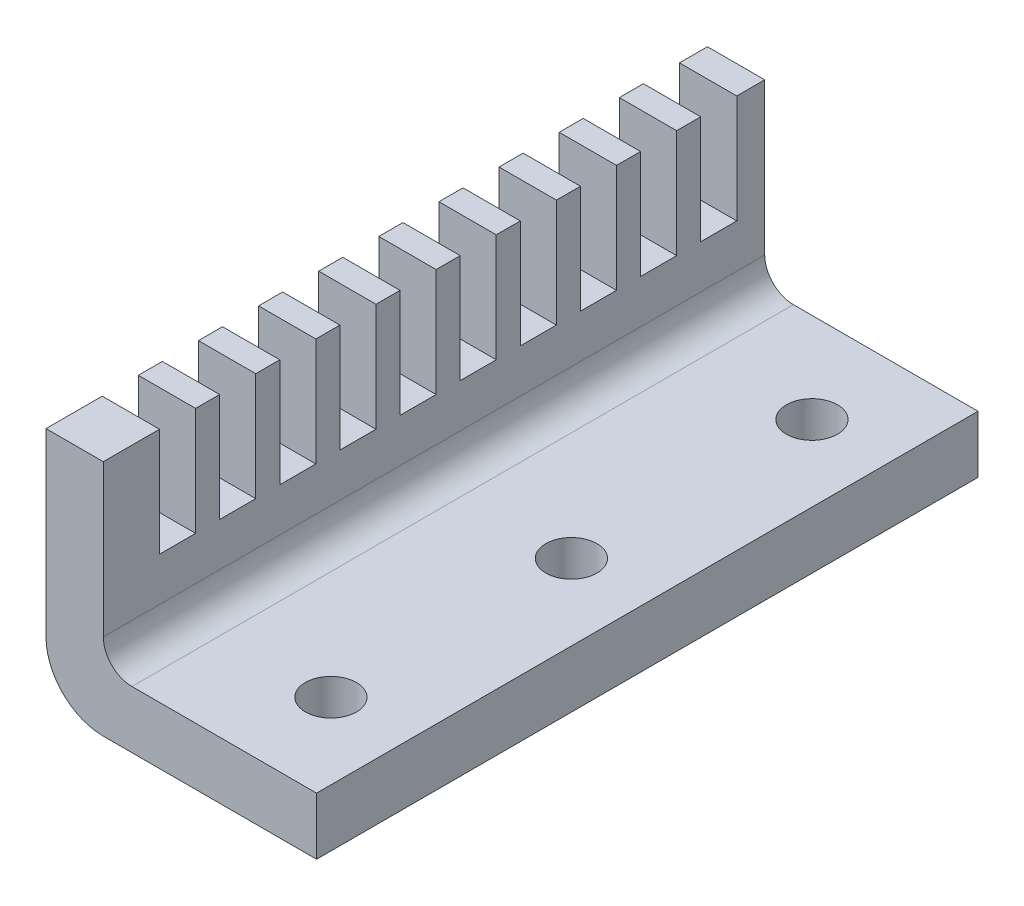
SolidWorks part; units mm, degrees
material "AISI 1045 Aço, trefilado"
ref_plane "Plano frontal" through (0, 0, 0) normal (0, 0, 1) x (1, 0, 0)
ref_plane "Plano superior" through (0, 0, 0) normal (0, 1, 0) x (1, 0, 0)
ref_plane "Plano direito" through (0, 0, 0) normal (1, 0, 0) x (0, 0, -1)
sketch "Esboço1" plane through (0, 0, 0) normal (0, 0, 1) x (1, 0, 0)
  line L0 (9.53, 0) -> (45, 0)
  line L1 (45, 0) -> (45, 9.53)
  line L2 (45, 9.53) -> (14.295, 9.53)
  line L3 (9.53, 14.295) -> (9.53, 39.53)
  line L4 (9.53, 39.53) -> (0, 39.53)
  line L5 (0, 39.53) -> (0, 9.53)
  arc A0 (14.295, 9.53) -> (9.53, 14.295) centre (14.295, 14.295) cw
  arc A1 (9.53, 0) -> (0, 9.53) centre (9.53, 9.53) cw
  point P11 (0, 0)
  dimension "D5" = 4.765
  dimension "D6" = 9.53
  dimension "D1" = 9.53
  dimension "D2" = 9.53
  dimension "D3" = 45
  dimension "D4" = 39.53
extrude "Ressalto-extrusão1" add sketch "Esboço1" along normal blind 110
sketch "Esboço2" plane through (9.53, 0, 0) normal (1, 0, 0) x (0, 0, -1)
  line L0 (0, 39.53) -> (-4.65, 39.53) construction
  line L1 (-10.65, 39.53) -> (-14.65, 39.53) construction
  line L2 (0, 14.295) -> (0, 39.53) construction
  line L3 (-110, 39.53) -> (0, 39.53) construction
  line L4 (-4.65, 39.53) -> (-4.65, 21.53)
  line L5 (-4.65, 21.53) -> (-10.65, 21.53)
  line L6 (-10.65, 21.53) -> (-10.65, 39.53)
  line L7 (-110, 39.53) -> (-100.65, 39.53) construction
  line L8 (-100.65, 39.53) -> (-100.65, 21.53)
  line L9 (-74.65, 21.53) -> (-80.65, 21.53)
  line L10 (-74.65, 21.53) -> (-74.65, 39.53)
  line L11 (-74.65, 39.53) -> (-70.65, 39.53) construction
  line L12 (-70.65, 39.53) -> (-70.65, 21.53)
  line L13 (-70.65, 21.53) -> (-64.65, 21.53)
  line L14 (-64.65, 21.53) -> (-64.65, 39.53)
  line L15 (-64.65, 39.53) -> (-60.65, 39.53) construction
  line L16 (-60.65, 39.53) -> (-60.65, 21.53)
  line L17 (-60.65, 21.53) -> (-54.65, 21.53)
  line L18 (-54.65, 21.53) -> (-54.65, 39.53)
  line L19 (-54.65, 39.53) -> (-50.65, 39.53) construction
  line L20 (-50.65, 39.53) -> (-50.65, 21.53)
  line L21 (-50.65, 21.53) -> (-44.65, 21.53)
  line L22 (-44.65, 21.53) -> (-44.65, 39.53)
  line L23 (-44.65, 39.53) -> (-40.65, 39.53) construction
  line L24 (-40.65, 39.53) -> (-40.65, 21.53)
  line L25 (-40.65, 21.53) -> (-34.65, 21.53)
  line L26 (-34.65, 21.53) -> (-34.65, 39.53)
  line L27 (-34.65, 39.53) -> (-30.65, 39.53) construction
  line L28 (-30.65, 39.53) -> (-30.65, 21.53)
  line L29 (-30.65, 21.53) -> (-24.65, 21.53)
  line L30 (-24.65, 21.53) -> (-24.65, 39.53)
  line L31 (-24.65, 39.53) -> (-20.65, 39.53) construction
  line L32 (-20.65, 39.53) -> (-20.65, 21.53)
  line L33 (-20.65, 21.53) -> (-14.65, 21.53)
  line L34 (-14.65, 21.53) -> (-14.65, 39.53)
  line L35 (-80.65, 21.53) -> (-80.65, 39.53)
  line L36 (-80.65, 39.53) -> (-84.65, 39.53) construction
  line L37 (-84.65, 39.53) -> (-84.65, 21.53)
  line L38 (-84.65, 21.53) -> (-90.65, 21.53)
  line L39 (-90.65, 21.53) -> (-90.65, 39.53)
  line L40 (-90.65, 39.53) -> (-94.65, 39.53) construction
  line L41 (-94.65, 39.53) -> (-94.65, 21.53)
  line L42 (-94.65, 21.53) -> (-100.65, 21.53)
  line L43 (-100.65, 39.53) -> (-94.65, 39.53)
  line L44 (-90.65, 39.53) -> (-84.65, 39.53)
  line L45 (-80.65, 39.53) -> (-74.65, 39.53)
  line L46 (-70.65, 39.53) -> (-64.65, 39.53)
  line L47 (-60.65, 39.53) -> (-54.65, 39.53)
  line L48 (-50.65, 39.53) -> (-44.65, 39.53)
  line L49 (-40.65, 39.53) -> (-34.65, 39.53)
  line L50 (-30.65, 39.53) -> (-24.65, 39.53)
  line L51 (-20.65, 39.53) -> (-14.65, 39.53)
  line L52 (-10.65, 39.53) -> (-4.65, 39.53)
  dimension "D1" = 4.65
  dimension "D2" = 18
  dimension "D3" = 6
  dimension "D4" = 4
  dimension "D5" = 4
  dimension "D6" = 4
  dimension "D7" = 4
  dimension "D8" = 4
  dimension "D9" = 4
  dimension "D10" = 4
  dimension "D11" = 9.35
  dimension "D12" = 6
  dimension "D13" = 6
  dimension "D14" = 6
  dimension "D15" = 6
  dimension "D16" = 6
  dimension "D17" = 6
  dimension "D18" = 6
  dimension "D19" = 6
  dimension "D20" = 6
  dimension "D21" = 4
  dimension "D22" = 4
extrude "Corte-extrusão1" cut sketch "Esboço2" against normal through all
hole_wizard "Broca de rosquear para tarraxa de M10x1.51" positions "3DSketch1" profile "Esboço4" hole size "M10x1.5" standard "Ansi Metric" end condition through all
sketch3d "3DSketch1"
  line L0 (45, 9.53, 0) -> (14.295, 9.53, 0) construction
  line L1 (45, 9.53, 110) -> (14.295, 9.53, 110) construction
  line L2 (45, 9.53, 110) -> (45, 9.53, 0) construction
  point P0 (32.38, 9.53, 15)
  point P2 (32.38, 9.53, 55)
  point P4 (32.38, 9.53, 95)
  dimension "D1" = 15
  dimension "D2" = 15
  dimension "D3" = 55
  dimension "D4" = 12.62
  dimension "D5" = 12.62
  dimension "D6" = 12.62
sketch "Esboço4" plane through (32.38, 9.53, 15) normal (1, 0, 0) x (0, 0, 1)
  line L0 (0, 0) -> (0, 9.53)
  line L1 (0, 9.53) -> (4.25, 9.53)
  line L2 (4.25, 9.53) -> (4.25, 0)
  line L5 (4.25, 0) -> (0, 0)
  line L11 (0, -6.35) -> (0, 107.95) construction
  dimension "Thru Hole Dia." = 8.5
  dimension "Thru Hole Depth" = 9.53
